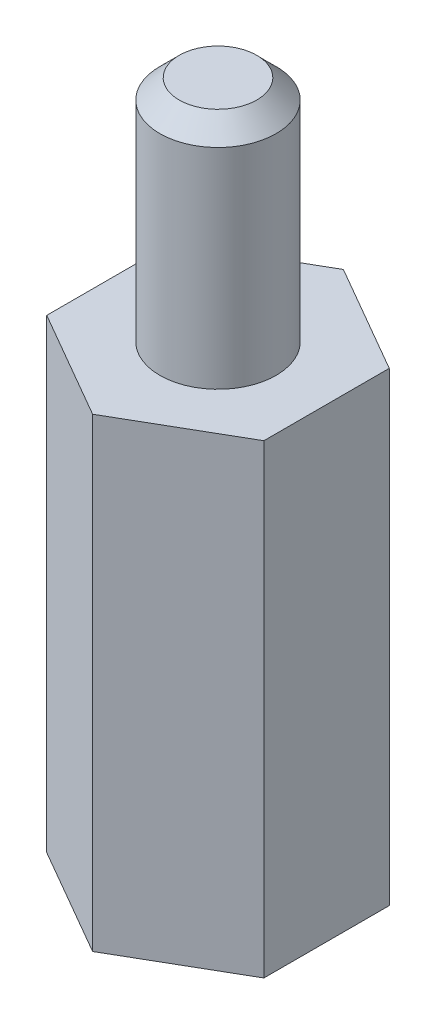
SolidWorks part; units mm, degrees
ref_plane "Front Plane" through (0, 0, 0) normal (0, 0, 1) x (1, 0, 0)
ref_plane "Top Plane" through (0, 0, 0) normal (0, 1, 0) x (1, 0, 0)
ref_plane "Right Plane" through (0, 0, 0) normal (1, 0, 0) x (0, 0, -1)
sketch "Sketch1" plane through (0, 0, 0) normal (0, 1, 0) x (1, 0, 0)
  line L1 (0, -3.2332) -> (2.8, -1.6166)
  line L2 (2.8, -1.6166) -> (2.8, 1.6166)
  line L3 (2.8, 1.6166) -> (0, 3.2332)
  line L4 (0, 3.2332) -> (-2.8, 1.6166)
  line L5 (-2.8, 1.6166) -> (-2.8, -1.6166)
  line L6 (-2.8, -1.6166) -> (0, -3.2332)
  circle A0 centre (0, 0) radius 2.8 construction
  dimension "D1" = 5.6
extrude "Boss-Extrude1" add sketch "Sketch1" along normal blind 12
sketch "Sketch2" plane through (0, 12, 0) normal (0, 1, 0) x (1, 0, 0)
  circle A0 centre (0, 0) radius 1.5
  dimension "D1" = 3
extrude "Boss-Extrude2" add sketch "Sketch2" along normal blind 5.9
sketch "Sketch3" plane through (0, 0, 0) normal (0, -1, 0) x (1, 0, 0)
  circle A0 centre (0, 0) radius 1.5
  dimension "D1" = 3
extrude "Cut-Extrude1" cut sketch "Sketch3" against normal offset from surface (10 mm away) 2 up to face at (0, 12, 1.5)
chamfer "Chamfer1" distance 0.5 angle 45 1 edges at (0, 17.9, 1.5)
